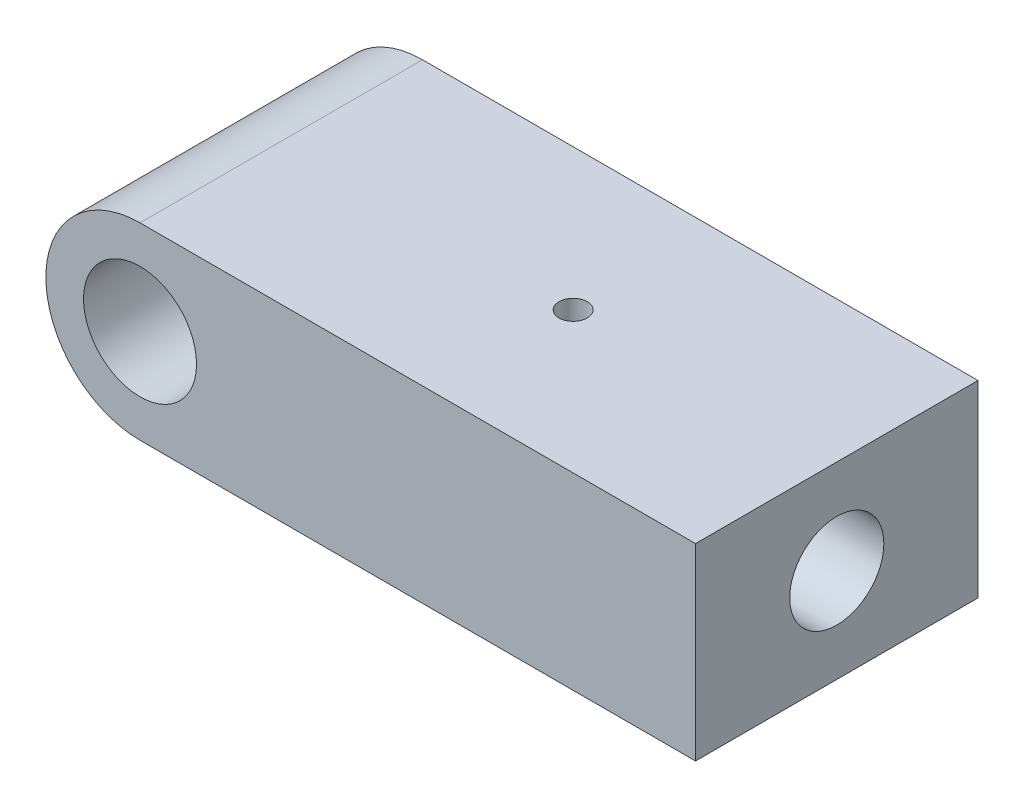
SolidWorks part; units mm, degrees
material "Alu 2017 (AU4G)"
ref_plane "Face" through (0, 0, 0) normal (0, 0, 1) x (1, 0, 0)
ref_plane "Dessus" through (0, 0, 0) normal (0, 1, 0) x (1, 0, 0)
ref_plane "Droite" through (0, 0, 0) normal (1, 0, 0) x (0, 0, -1)
sketch "Esquisse1" plane through (0, 0, 0) normal (0, 0, 1) x (1, 0, 0)
  line L0 (0, -10) -> (59, -10)
  line L2 (0, 10) -> (59, 10)
  line L3 (59, 10) -> (59, -10)
  arc A0 (0, 10) -> (0, -10) centre (0, 0) ccw
  circle A1 centre (0, 0) radius 6
  dimension "D3" = 12
  dimension "D1" = 20
  dimension "D2" = 59
extrude "Boss.-Extru.1" add sketch "Esquisse1" along normal mid plane 30
hole_wizard "Diamètre du perçage Ø10.0 (10)1" positions "Esquisse4" profile "Esquisse3" hole size "Ø10.0" standard "ISO"
sketch "Esquisse4" plane through (59, 0, 0) normal (1, 0, 0) x (0, 0, -1)
  point P0 (0, 0)
sketch "Esquisse3" plane through (59, 0, 0) normal (0, 1, 0) x (0, 0, -1)
  line L0 (0, 0) -> (0, 40)
  line L1 (0, 40) -> (5, 40)
  line L2 (5, 40) -> (5, 0)
  line L5 (5, 0) -> (0, 0)
  line L10 (0, 40) -> (-5, 40) construction
  line L11 (0, -6.35) -> (0, 107.95) construction
  dimension "Diamètre du perçage" = 10
  dimension "Profondeur du perçage" = 40
  dimension "Angle de pointe" = 180
hole_wizard "Diamètre du perçage Ø3.0 (3)1" positions "Esquisse6" profile "Esquisse5" hole size "Ø3.0" standard "ISO"
sketch "Esquisse6" plane through (0, 10, 0) normal (0, 1, 0) x (1, 0, 0)
  line L0 (59, -15) -> (59, 15) construction
  point P0 (31, 0)
  dimension "D1" = 28
sketch "Esquisse5" plane through (31, 10, 0) normal (1, 0, 0) x (0, 0, 1)
  line L0 (0, 0) -> (0, 10.9013)
  line L1 (0, 10.9013) -> (1.5, 10)
  line L2 (1.5, 10) -> (1.5, 0)
  line L5 (1.5, 0) -> (0, 0)
  line L10 (0, 10.9013) -> (-1.5, 10) construction
  line L11 (0, -6.35) -> (0, 107.95) construction
  dimension "Diamètre du perçage" = 3
  dimension "Profondeur du perçage" = 10
  dimension "Angle de pointe" = 118
